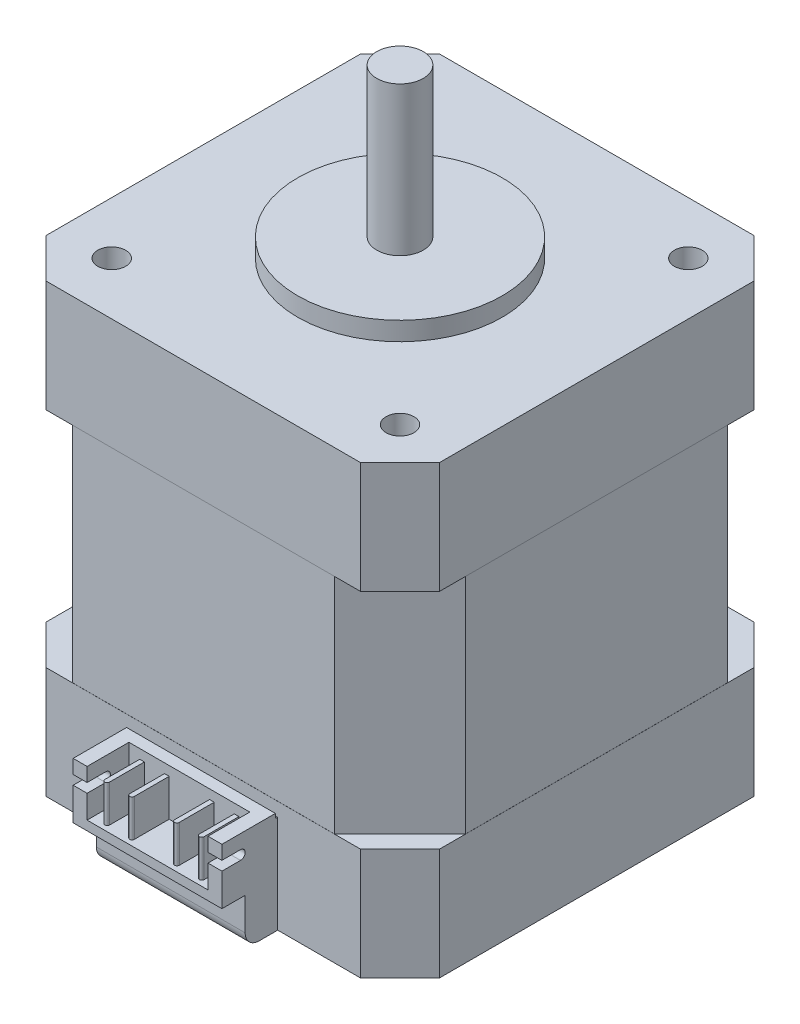
SolidWorks part; units mm, degrees
material "1060 Alloy"
ref_plane "Front Plane" through (0, 0, 0) normal (0, 0, 1) x (1, 0, 0)
ref_plane "Top Plane" through (0, 0, 0) normal (0, 1, 0) x (1, 0, 0)
ref_plane "Right Plane" through (0, 0, 0) normal (1, 0, 0) x (0, 0, -1)
sketch "Sketch1" plane through (0, 0, 0) normal (0, 1, 0) x (1, 0, 0)
  line L9 (-21.15, -21.15) -> (21.15, -21.15)
  line L10 (-21.15, -21.15) -> (-21.15, 21.15)
  line L11 (-21.15, 21.15) -> (21.15, 21.15)
  line L12 (21.15, -21.15) -> (21.15, 21.15)
  line L13 (-21.15, -21.15) -> (21.15, 21.15) construction
  line L14 (-21.15, 21.15) -> (21.15, -21.15) construction
  point P0 (0, 0)
  dimension "D1" = 42.3
extrude "Boss-Extrude1" add sketch "Sketch1" along normal blind 48
sketch "Sketch2" plane through (0, 48, 0) normal (0, 1, 0) x (1, 0, 0)
  circle A0 centre (0, 0) radius 11
  dimension "D1" = 22
extrude "Boss-Extrude2" add sketch "Sketch2" along normal blind 2
sketch "Sketch3" plane through (0, 50, 0) normal (0, 1, 0) x (1, 0, 0)
  circle A0 centre (0, 0) radius 2.5
  dimension "D1" = 5
extrude "Boss-Extrude3" add sketch "Sketch3" along normal blind 16
sketch "Sketch4" plane through (0, 48, 0) normal (0, 1, 0) x (1, 0, 0)
  line L0 (-21.15, 16.9074) -> (-16.9074, 21.15)
  line L1 (-21.15, 21.15) -> (-21.15, -21.15) construction
  line L2 (21.15, 21.15) -> (-21.15, 21.15) construction
  line L3 (-16.9074, 21.15) -> (-21.15, 21.15)
  line L4 (-21.15, 21.15) -> (-21.15, 16.9074)
  line L5 (0, 0) -> (0, 27.6659) construction
  line L6 (21.15, 21.15) -> (21.15, 16.9074)
  line L7 (16.9074, 21.15) -> (21.15, 21.15)
  line L8 (21.15, 16.9074) -> (16.9074, 21.15)
  line L9 (0, 0) -> (-36.313, 0) construction
  line L10 (21.15, -16.9074) -> (16.9074, -21.15)
  line L11 (16.9074, -21.15) -> (21.15, -21.15)
  line L12 (21.15, -21.15) -> (21.15, -16.9074)
  line L13 (-21.15, -21.15) -> (-21.15, -16.9074)
  line L14 (-16.9074, -21.15) -> (-21.15, -21.15)
  line L15 (-21.15, -16.9074) -> (-16.9074, -21.15)
  dimension "D1" = 45
  dimension "D2" = 6
extrude "Cut-Extrude1" cut sketch "Sketch4" against normal through all both and the other way through all
sketch "Sketch5" plane through (21.15, 0, 0) normal (1, 0, 0) x (0, 0, -1)
  line L0 (-16.9074, 0) -> (-16.9074, 48) construction
  line L1 (16.9074, 12) -> (-16.9074, 12)
  line L2 (16.9074, 12) -> (16.9074, 36)
  line L3 (16.9074, 36) -> (-16.9074, 36)
  line L4 (-16.9074, 12) -> (-16.9074, 36)
  line L5 (16.9074, 12) -> (-16.9074, 36) construction
  line L6 (16.9074, 36) -> (-16.9074, 12) construction
  line L7 (-16.9074, 0) -> (16.9074, 0) construction
  line L8 (-16.9074, 48) -> (16.9074, 48) construction
  line L9 (16.9074, 0) -> (16.9074, 48) construction
  point P0 (0, 24)
  dimension "D1" = 12
  dimension "D2" = 12
extrude "Cut-Extrude2" cut sketch "Sketch5" against normal blind 0.01
sketch "Sketch6" plane through (0, 48, 0) normal (0, 1, 0) x (1, 0, 0)
  line L0 (21.15, 14.0789) -> (14.0789, 21.15)
  line L1 (21.15, -16.9074) -> (21.15, 16.9074) construction
  line L2 (16.9074, 21.15) -> (-16.9074, 21.15) construction
  line L3 (14.0789, 21.15) -> (21.15, 21.15)
  line L4 (21.15, 21.15) -> (21.15, 14.0789)
  dimension "D1" = 10
  dimension "D2" = 45
extrude "Cut-Extrude3" cut sketch "Sketch6" against normal up to surface (24 mm away) from surface at -12 up to face at (21.145, 12, 0) starting at face at (21.145, 36, 0)
pattern_circular "CirPattern1" count 4 over 360 about axis through (0, 0, 0) along (0, 1, 0) of "Cut-Extrude2", "Cut-Extrude3"
sketch "Sketch7" plane through (0, 48, 0) normal (0, 1, 0) x (1, 0, 0)
  circle A0 centre (15.5, 15.5) radius 1.5
  circle A1 centre (15.5, -15.5) radius 1.5
  circle A2 centre (-15.5, -15.5) radius 1.5
  circle A3 centre (-15.5, 15.5) radius 1.5
  point P12 (0, 0)
  dimension "D3" = 3
  dimension "D5" = 31
  dimension "D1" = 15.5
  dimension "D2" = 15.5
  dimension "D4" = 4
extrude "Cut-Extrude4" cut sketch "Sketch7" against normal blind 4.5
sketch "Sketch8" plane through (0, 0, 21.15) normal (0, 0, 1) x (1, 0, 0)
  line L0 (-16.9074, 0) -> (16.9074, 0) construction
  line L1 (-8, 0) -> (8, 0)
  line L2 (-8, 0) -> (-8, 11)
  line L3 (-8, 11) -> (8, 11)
  line L4 (8, 0) -> (8, 11)
  dimension "D1" = 16
  dimension "D2" = 11
extrude "Boss-Extrude4" add sketch "Sketch8" along normal blind 6
sketch "Sketch9" plane through (0, 0, 27.15) normal (0, 0, 1) x (1, 0, 0)
  line L0 (8, 0) -> (8, 11) construction
  line L1 (-8, 0) -> (8, 0)
  line L2 (-8, 0) -> (-8, 5)
  line L3 (-8, 5) -> (8, 5)
  line L4 (8, 0) -> (8, 5)
  dimension "D1" = 5
extrude "Cut-Extrude5" cut sketch "Sketch9" against normal blind 2.5
fillet "Fillet1" radius 1.5 1 edges at (0, 0, 24.65)
sketch "Sketch10" plane through (0, 11, 0) normal (0, 1, 0) x (1, 0, 0)
  line L0 (8, -27.15) -> (-8, -27.15) construction
  line L1 (-6.5, -27.15) -> (6.5, -27.15)
  line L2 (-6.5, -27.15) -> (-6.5, -22.65)
  line L3 (-6.5, -22.65) -> (6.5, -22.65)
  line L4 (6.5, -27.15) -> (6.5, -22.65)
  point P6 (0, -27.15)
  dimension "D1" = 13
  dimension "D2" = 4.5
extrude "Cut-Extrude6" cut sketch "Sketch10" against normal blind 5
sketch "Sketch11" plane through (8, 0, 0) normal (1, 0, 0) x (0, 0, -1)
  line L0 (-27.15, 5) -> (-27.15, 11) construction
  line L1 (-27.15, 11) -> (-21.15, 11) construction
  line L2 (-27.15, 9.5) -> (-25.15, 9.5)
  line L3 (-27.15, 9.5) -> (-27.15, 8.5)
  line L4 (-27.15, 8.5) -> (-25.15, 8.5)
  arc A0 (-25.15, 8.5) -> (-25.15, 9.5) centre (-25.15, 9) ccw
  point P5 (-24.65, 9)
  dimension "D2" = 1.5
  dimension "D1" = 1
extrude "Cut-Extrude7" cut sketch "Sketch11" against normal through all
sketch "Sketch12" plane through (0, 6, 0) normal (0, 1, 0) x (1, 0, 0)
  line L0 (0, 5.4741) -> (0, -32.9784) construction
  line L1 (6.5, -22.65) -> (-6.5, -22.65) construction
  line L2 (-2.667, -22.65) -> (-2.167, -22.65)
  line L3 (-2.667, -22.65) -> (-2.667, -26.4)
  line L5 (-2.167, -22.65) -> (-2.167, -26.4)
  line L8 (5.334, -22.65) -> (5.334, -26.4)
  line L9 (-4.834, -22.65) -> (-5.334, -22.65)
  line L10 (-4.834, -22.65) -> (-4.834, -26.4)
  line L12 (-5.334, -22.65) -> (-5.334, -26.4)
  line L13 (4.834, -22.65) -> (4.834, -26.4)
  line L14 (4.834, -22.65) -> (5.334, -22.65)
  line L15 (2.167, -22.65) -> (2.167, -26.4)
  line L16 (2.667, -22.65) -> (2.667, -26.4)
  line L17 (2.667, -22.65) -> (2.167, -22.65)
  arc A0 (-5.334, -26.4) -> (-4.834, -26.4) centre (-5.084, -26.4) ccw
  arc A1 (-2.667, -26.4) -> (-2.167, -26.4) centre (-2.417, -26.4) ccw
  arc A2 (2.667, -26.4) -> (2.167, -26.4) centre (2.417, -26.4) cw
  arc A3 (5.334, -26.4) -> (4.834, -26.4) centre (5.084, -26.4) cw
  point P4 (-2.417, -26.65)
  point P11 (-5.084, -26.65)
  dimension "D7" = 0.25
  dimension "D1" = 0.25
  dimension "D2" = 0.5
  dimension "D3" = 2.167
  dimension "D4" = 4
  dimension "D5" = 0.5
  dimension "D6" = 2.167
  dimension "D8" = 4
extrude "Boss-Extrude5" add sketch "Sketch12" along normal blind 4
sketch "Sketch13" plane through (0, 11, 0) normal (0, 1, 0) x (1, 0, 0)
  line L0 (8, -27.15) -> (8, -21.15) construction
  line L1 (-8, -21.15) -> (8, -21.15)
  line L2 (-8, -21.15) -> (-8, -21.4)
  line L3 (-8, -21.4) -> (8, -21.4)
  line L4 (8, -21.15) -> (8, -21.4)
  dimension "D1" = 0.25
extrude "Cut-Extrude8" cut sketch "Sketch13" against normal blind 0.5
fillet "Fillet2" radius 0.125 1 edges at (0, 10.5, 21.4)
